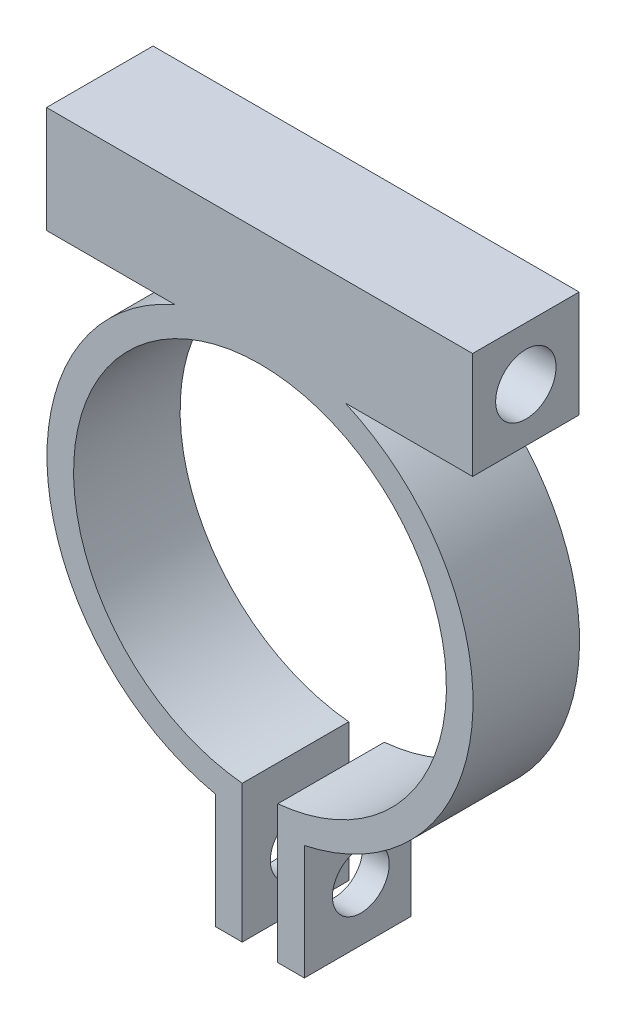
SolidWorks part; units mm, degrees
ref_plane "Alzado" through (0, 0, 0) normal (0, 0, 1) x (1, 0, 0)
ref_plane "Planta" through (0, 0, 0) normal (0, 1, 0) x (1, 0, 0)
ref_plane "Vista lateral" through (0, 0, 0) normal (1, 0, 0) x (0, 0, -1)
sketch "Croquis1" plane through (0, 0, 0) normal (0, 0, 1) x (1, 0, 0)
  line L1 (11.9755, 17) -> (-12.0245, 17)
  line L2 (11.9755, 17) -> (11.9755, 11)
  line L3 (11.9755, 11) -> (-12.0245, 11)
  line L4 (-12.0245, 17) -> (-12.0245, 11)
  line L5 (11.9755, 17) -> (-12.0245, 11) construction
  line L6 (11.9755, 11) -> (-12.0245, 17) construction
  line L7 (1, -16.2575) -> (-1, -16.2575)
  line L8 (1, -16.2575) -> (1, -6.1463)
  line L9 (1, -6.1463) -> (-1, -6.1463)
  line L10 (-1, -16.2575) -> (-1, -6.1463)
  line L11 (1, -16.2575) -> (-1, -6.1463) construction
  line L12 (1, -6.1463) -> (-1, -16.2575) construction
  line L13 (1, -11.2019) -> (2.5, -11.2019)
  line L14 (1, -11.2019) -> (1, -18.2019)
  line L15 (1, -18.2019) -> (2.5, -18.2019)
  line L16 (2.5, -11.2019) -> (2.5, -18.2019)
  line L17 (-1, -11.2019) -> (-2.5, -11.2019)
  line L18 (-1, -11.2019) -> (-1, -18.2019)
  line L19 (-1, -18.2019) -> (-2.5, -18.2019)
  line L20 (-2.5, -11.2019) -> (-2.5, -18.2019)
  circle A0 centre (0, 0) radius 10.5
  circle A1 centre (0, 0) radius 12
  point P4 (-0.0245, 14)
  point P9 (0, -11.2019)
  dimension "D1" = 21
  dimension "D2" = 24
  dimension "D3" = 6
  dimension "D4" = 24
  dimension "D5" = 14
  dimension "D6" = 2
  dimension "D7" = 1.5
  dimension "D8" = 1.5
  dimension "D9" = 7
extrude "Saliente-Extruir1" add sketch "Croquis1" along normal blind 6 contours L3 A1 A0 | A1 L3 L2 L1 L4 | L3 A1 | L18 L17 L20 L19 | L14 L13 L16 L15
sketch "Croquis4" plane through (11.9755, 0, 0) normal (1, 0, 0) x (0, 0, -1)
  point P0 (-3, 14)
hole_wizard "Taladro de margen para M31" positions "Croquis7" profile "Croquis6" hole size "M3" standard "Ansi Metric" end condition through all
sketch "Croquis7" plane through (11.9755, 0, 0) normal (1, 0, 0) x (0, 0, -1)
  point P0 (-3, 14)
sketch "Croquis6" plane through (11.9755, 14, 3) normal (0, 1, 0) x (0, 0, -1)
  line L0 (0, 0) -> (0, 24)
  line L1 (0, 24) -> (1.7, 24)
  line L2 (1.7, 24) -> (1.7, 0)
  line L5 (1.7, 0) -> (0, 0)
  line L11 (0, -6.35) -> (0, 107.95) construction
  dimension "Diámetro de taladro hasta el siguiente" = 3.4
  dimension "Profundidad de taladro hasta el siguiente" = 24
hole_wizard "Taladro de margen para M32" positions "Croquis10" profile "Croquis11" hole size "M3" standard "Ansi Metric" end condition through all
sketch "Croquis10" plane through (-2.5, 0, 0) normal (-1, 0, 0) x (0, 0, 1)
  point P0 (2.8205, -15.0239)
sketch "Croquis11" plane through (-2.5, -15.0239, 2.8205) normal (0, 1, 0) x (0, 0, 1)
  line L0 (0, 0) -> (0, 14.5)
  line L1 (0, 14.5) -> (1.6, 14.5)
  line L2 (1.6, 14.5) -> (1.6, 0)
  line L5 (1.6, 0) -> (0, 0)
  line L11 (0, -6.35) -> (0, 107.95) construction
  dimension "Diámetro de taladro hasta el siguiente" = 3.2
  dimension "Profundidad de taladro hasta el siguiente" = 14.5
